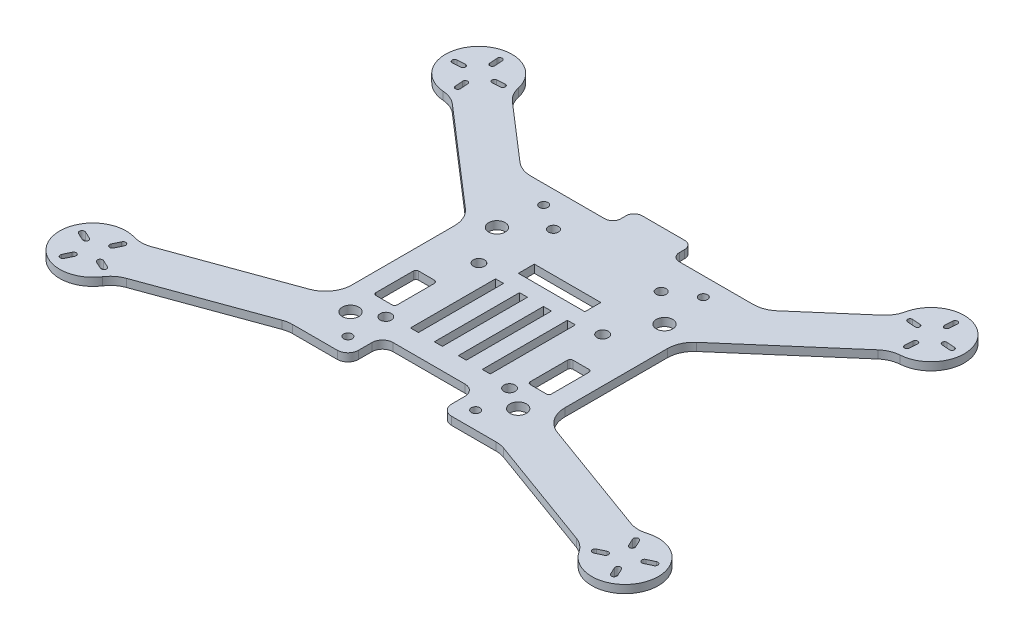
SolidWorks part; units mm, degrees
material "Thornel Mat VMA"
ref_plane "Front Plane" through (0, 0, 0) normal (0, 0, 1) x (1, 0, 0)
ref_plane "Top Plane" through (0, 0, 0) normal (0, 1, 0) x (1, 0, 0)
ref_plane "Right Plane" through (0, 0, 0) normal (1, 0, 0) x (0, 0, -1)
sketch "Sketch1" plane through (0, 0, 0) normal (0, 1, 0) x (1, 0, 0)
  line L0 (0, 0) -> (0, -25922.3753) construction
  line L1 (0, 0) -> (50000, 0) construction
  line L2 (0.0146, -0.0126) -> (37798.4826, -32730.3627) construction
  line L7 (-40, 24.0543) -> (-82.976, 61.2679)
  line L8 (-45.5212, 50) -> (-72.5023, 73.3634)
  line L9 (-0.0841, -0.0728) -> (-37798.5521, -32730.4229) construction
  line L10 (-40, -24.0543) -> (-82.976, -61.2679) construction
  line L11 (-45.5212, -50) -> (-72.5023, -73.3634) construction
  line L12 (45.5212, -50) -> (72.5023, -73.3634) construction
  line L13 (40, -24.0543) -> (82.976, -61.2679) construction
  line L14 (40, 24.0543) -> (82.976, 61.2679)
  line L15 (45.5212, 50) -> (72.5023, 73.3634)
  line L16 (-40, 24.0543) -> (-40, -24.0543) construction
  line L17 (-45.5212, 50) -> (45.5212, 50)
  line L18 (-45.5212, -50) -> (45.5212, -50) construction
  line L19 (40, 24.0543) -> (40, -24.0543) construction
  line L20 (10.4319, -16.2031) -> (-46974.1992, -17117.2103) construction
  line L21 (-10.0613, -15.3084) -> (45305.3281, -21146.2214) construction
  line L22 (-40, -26.0454) -> (-93.7107, -45.5945)
  line L23 (-40, 24.0543) -> (-40, -26.0454)
  line L24 (-40, -43.0722) -> (-88.2384, -60.6296)
  line L25 (-40, -43.0722) -> (40, -43.0722)
  line L26 (40, -43.0722) -> (88.2384, -60.6296)
  line L27 (40, -26.0454) -> (93.7107, -45.5945)
  line L28 (40, 24.0543) -> (40, -26.0454)
  arc A0 (-72.5023, 73.3634) -> (-82.976, 61.2679) centre (-85, 73.603) ccw
  arc A1 (82.976, 61.2679) -> (72.5023, 73.3634) centre (85, 73.603) ccw
  arc A2 (-82.976, -61.2679) -> (-72.5023, -73.3634) centre (-85, -73.603) ccw construction
  arc A3 (72.5023, -73.3634) -> (82.976, -61.2679) centre (85, -73.603) ccw construction
  arc A4 (-93.7107, -45.5945) -> (-88.2384, -60.6296) centre (-100, -56.397) ccw
  arc A5 (93.7107, -45.5945) -> (88.2384, -60.6296) centre (100, -56.397) cw
  point P44 (0, -43.0722)
  point P45 (0, -20)
  dimension "D2" = 25
  dimension "D3" = 16
  dimension "D1" = 170
  dimension "D4" = 130
  dimension "D5" = 40
  dimension "D6" = 50
  dimension "D7" = 70
  dimension "D8" = 65
  dimension "D9" = 16
  dimension "D10" = 100
  dimension "D11" = 20
extrude "Boss-Extrude1" add sketch "Sketch1" along normal blind 3
fillet "Fillet1" radius 10 8 edges at (45.5212, 1.5, -50) (-45.5212, 1.5, -50) (-40, 1.5, -24.0543) (40, 1.5, -24.0543) (40, 1.5, 26.0454) (40, 1.5, 43.0722) (-40, 1.5, 43.0722) (-40, 1.5, 26.0454)
fillet "Fillet2" radius 10 8 edges at (-72.5023, 1.5, -73.3634) (82.976, 1.5, -61.2679) (72.5023, 1.5, -73.3634) (-82.976, 1.5, -61.2679) (88.2384, 1.5, 60.6296) (93.7107, 1.5, 45.5945) (-93.7107, 1.5, 45.5945) (-88.2384, 1.5, 60.6296)
sketch "Sketch3" plane through (0, 3, 0) normal (0, 1, 0) x (1, 0, 0)
  line L0 (0, 0) -> (0, -50000) construction
  line L2 (-38.2367, -43.0722) -> (38.2367, -43.0722) construction
  circle A0 centre (-23.25, -23.0722) radius 2.11
  circle A1 centre (23.25, -23.0722) radius 2.11
  circle A2 centre (23.25, 11.9278) radius 2.11
  circle A3 centre (-23.25, 11.9278) radius 2.11
  dimension "D3" = 4.22
  dimension "D1" = 46.5
  dimension "D2" = 35
  dimension "D4" = 20
extrude "Cut-Extrude2" cut sketch "Sketch3" against normal through all
sketch "Sketch4" plane through (0, 3, 0) normal (0, 1, 0) x (1, 0, 0)
  line L0 (0, 0) -> (0, -50000) construction
  line L2 (-38.2367, -43.0722) -> (38.2367, -43.0722) construction
  circle A0 centre (-23.5, -36.0722) radius 1.1
  circle A1 centre (23.5, -36.0722) radius 1.1
  dimension "D3" = 2.2
  dimension "D1" = 47
  dimension "D2" = 7
extrude "Cut-Extrude3" [suppressed] cut sketch "Sketch4" against normal through all
sketch "Sketch5" plane through (0, 0, 0) normal (0, -1, 0) x (1, 0, 0)
  line L0 (0, -8.4275) -> (0, 49991.5725) construction
  line L1 (-11, 43.0722) -> (-11, 36.5722)
  line L3 (-11, 36.5722) -> (-4.5, 29.5722)
  line L4 (-4.5, 29.5722) -> (-4.5, 18.5722)
  line L5 (-4.5, 18.5722) -> (4.5, 18.5722)
  line L6 (-11, 43.0722) -> (11, 43.0722)
  line L7 (4.5, 29.5722) -> (4.5, 18.5722)
  line L8 (11, 36.5722) -> (4.5, 29.5722)
  line L9 (11, 43.0722) -> (11, 36.5722)
  line L10 (-38.2367, 43.0722) -> (38.2367, 43.0722) construction
  point P12 (0, 43.0722)
  point P13 (0, 18.5722)
  dimension "D1" = 11
  dimension "D2" = 6.5
  dimension "D3" = 24.5
  dimension "D4" = 11
  dimension "D5" = 4.5
extrude "Cut-Extrude4" [suppressed] cut sketch "Sketch5" against normal through all
sketch "Sketch6" plane through (0, 3, 0) normal (0, 1, 0) x (1, 0, 0)
  line L0 (0, 0) -> (0, -50000) construction
  line L2 (-38.2367, -43.0722) -> (38.2367, -43.0722) construction
  circle A0 centre (23.25, 25.9278) radius 2.11
  circle A1 centre (-23.25, 25.9278) radius 2.11
  circle A2 centre (-23.25, -9.0722) radius 2.11
  circle A3 centre (23.25, -9.0722) radius 2.11
  dimension "D3" = 4.22
  dimension "D1" = 46.5
  dimension "D2" = 35
  dimension "D4" = 34
extrude "Cut-Extrude5" [suppressed] cut sketch "Sketch6" against normal through all
sketch "Sketch7" plane through (0, 0, 0) normal (0, -1, 0) x (1, 0, 0)
  line L0 (0, 0) -> (0, -50000) construction
  line L1 (-17.5, 43.0722) -> (-17.5, 30.0722)
  line L2 (-38.2367, 43.0722) -> (38.2367, 43.0722) construction
  line L3 (-17.5, 30.0722) -> (17.5, 30.0722)
  line L4 (17.5, 30.0722) -> (17.5, 43.0722)
  line L5 (17.5, 43.0722) -> (-17.5, 43.0722)
  dimension "D1" = 35
  dimension "D2" = 13
extrude "Cut-Extrude6" cut sketch "Sketch7" against normal through all
fillet "Fillet3" radius 4 4 edges at (17.5, 1.5, 30.0722) (17.5, 1.5, 43.0722) (-17.5, 1.5, 30.0722) (-17.5, 1.5, 43.0722)
sketch "Sketch8" plane through (0, 3, 0) normal (0, 1, 0) x (1, 0, 0)
  line L0 (0, 0) -> (0, -50000) construction
  line L1 (-38.2367, -43.0722) -> (-21.5, -43.0722) construction
  circle A0 centre (-31.5, -28.0722) radius 3.1
  circle A1 centre (31.5, -28.0722) radius 3.1
  circle A2 centre (-31.5, 26.9278) radius 3.1
  circle A3 centre (31.5, 26.9278) radius 3.1
  dimension "D1" = 6.2
  dimension "D2" = 63
  dimension "D3" = 55
  dimension "D4" = 15
extrude "Cut-Extrude7" cut sketch "Sketch8" against normal through all
sketch "Sketch9" plane through (0, 3, 0) normal (0, 1, 0) x (1, 0, 0)
  line L0 (0, -0.8752) -> (0, -50000.8752) construction
  line L1 (-38.2367, -43.0722) -> (-21.5, -43.0722) construction
  circle A0 centre (-20.25, 36.9278) radius 1.875
  circle A1 centre (20.25, 36.9278) radius 1.875
  dimension "D1" = 3.75
  dimension "D2" = 40.5
  dimension "D3" = 80
extrude "Cut-Extrude8" cut sketch "Sketch9" against normal through all
sketch "Sketch10" plane through (0, 3, 0) normal (0, 1, 0) x (1, 0, 0)
  line L0 (41.7933, 50) -> (-41.7933, 50) construction
  line L1 (-11, 50) -> (11, 50)
  line L2 (-11, 50) -> (-11, 58)
  line L3 (-11, 58) -> (11, 58)
  line L4 (11, 50) -> (11, 58)
  point P6 (0, 58)
  dimension "D1" = 22
  dimension "D2" = 8
extrude "Boss-Extrude2" add sketch "Sketch10" against normal up to surface (3 mm away) up to face at (-20.25, 0, -35.0528)
fillet "Fillet4" radius 3 4 edges at (11, 1.5, -50) (11, 1.5, -58) (-11, 1.5, -58) (-11, 1.5, -50)
sketch "Sketch11" plane through (0, 3, 0) normal (0, 1, 0) x (1, 0, 0)
  line L0 (0, 0) -> (0, -50000) construction
  line L1 (-33, -2) -> (-25, -2)
  line L2 (-33, -2) -> (-33, -18)
  line L3 (-33, -18) -> (-25, -18)
  line L4 (-25, -2) -> (-25, -18)
  line L5 (25, -2) -> (25, -18)
  line L6 (33, -18) -> (25, -18)
  line L7 (33, -2) -> (33, -18)
  line L8 (33, -2) -> (25, -2)
  dimension "D1" = 8
  dimension "D2" = 16
  dimension "D3" = 25
  dimension "D4" = 2
extrude "Cut-Extrude9" cut sketch "Sketch11" against normal through all
fillet "Fillet5" radius 1 8 edges at (33, 1.5, 18) (25, 1.5, 18) (25, 1.5, 2) (33, 1.5, 2) (-25, 1.5, 18) (-33, 1.5, 18) (-33, 1.5, 2) (-25, 1.5, 2)
sketch "Sketch12" plane through (0, 3, 0) normal (0, 1, 0) x (1, 0, 0)
  line L0 (0, 0) -> (0, -50000) construction
  line L1 (-38.2367, -43.0722) -> (-21.5, -43.0722) construction
  circle A0 centre (-30, 43) radius 1.6
  circle A1 centre (30, 43) radius 1.6
  circle A2 centre (-24, -36.5722) radius 1.6
  circle A3 centre (24, -36.5722) radius 1.6
  dimension "D1" = 3.2
  dimension "D2" = 60
  dimension "D3" = 43
  dimension "D4" = 6.5
  dimension "D5" = 24
extrude "Cut-Extrude10" cut sketch "Sketch12" against normal through all
sketch "Sketch13" plane through (0, 3, 0) normal (0, 1, 0) x (1, 0, 0)
  line L0 (0, 0) -> (0, -50000) construction
  line L1 (-13.5, -30.0722) -> (13.5, -30.0722) construction
  line L2 (-15, 9.9278) -> (-12, 9.9278)
  line L3 (-15, 9.9278) -> (-15, -22.0722)
  line L4 (-15, -22.0722) -> (-12, -22.0722)
  line L5 (-12, 9.9278) -> (-12, -22.0722)
  line L6 (-6, 9.9278) -> (-6, -22.0722)
  line L7 (-6, 9.9278) -> (-3, 9.9278)
  line L8 (-3, 9.9278) -> (-3, -22.0722)
  line L9 (-6, -22.0722) -> (-3, -22.0722)
  line L10 (3, 9.9278) -> (3, -22.0722)
  line L11 (3, 9.9278) -> (6, 9.9278)
  line L12 (6, 9.9278) -> (6, -22.0722)
  line L13 (3, -22.0722) -> (6, -22.0722)
  line L14 (12, 9.9278) -> (12, -22.0722)
  line L15 (12, 9.9278) -> (15, 9.9278)
  line L16 (15, 9.9278) -> (15, -22.0722)
  line L17 (12, -22.0722) -> (15, -22.0722)
  dimension "D1" = 3
  dimension "D2" = 15
  dimension "D3" = 32
  dimension "D4" = 8
  dimension "D6" = 9
  dimension "D5" = 4
extrude "Cut-Extrude11" cut sketch "Sketch13" against normal through all
sketch "Sketch14" plane through (0, 3, 0) normal (0, 1, 0) x (1, 0, 0)
  line L0 (-80.023, 69.2933) -> (37643.1982, -32595.8992) construction
  line L1 (-48.3393, 52.4403) -> (-69.5576, 70.8135) construction
  line L2 (-85.6092, 82.0811) -> (-84.3908, 65.1248) construction
  line L3 (-93.4781, 72.9937) -> (-76.5219, 74.2122) construction
  line L4 (-85.6092, 82.0811) -> (-85.3942, 79.0888) construction
  line L5 (-84.7115, 82.1456) -> (-84.4965, 79.1533)
  line L6 (-86.5069, 82.0166) -> (-86.2919, 79.0243)
  line L7 (-93.4781, 72.9937) -> (-90.4859, 73.2088) construction
  line L8 (-93.5426, 73.8914) -> (-90.5504, 74.1065)
  line L9 (-93.4136, 72.0961) -> (-90.4213, 72.3111)
  line L10 (-84.3908, 65.1248) -> (-84.6058, 68.1171) construction
  line L11 (-83.4931, 65.1893) -> (-83.7081, 68.1816)
  line L12 (-85.2885, 65.0603) -> (-85.5035, 68.0526)
  line L13 (-76.5219, 74.2122) -> (-79.5141, 73.9972) construction
  line L14 (-76.5864, 75.1099) -> (-79.5787, 74.8949)
  line L15 (-76.4574, 73.3145) -> (-79.4496, 73.0995)
  line L16 (0, 0) -> (0, -50000) construction
  line L17 (85.6092, 82.0811) -> (85.3942, 79.0888) construction
  line L18 (84.7115, 82.1456) -> (84.4965, 79.1533)
  line L19 (86.5069, 82.0166) -> (86.2919, 79.0243)
  line L20 (93.4781, 72.9937) -> (90.4859, 73.2088) construction
  line L21 (93.5426, 73.8914) -> (90.5504, 74.1065)
  line L22 (93.4136, 72.0961) -> (90.4213, 72.3111)
  line L23 (84.3908, 65.1248) -> (84.6058, 68.1171) construction
  line L24 (83.4931, 65.1893) -> (83.7081, 68.1816)
  line L25 (85.2885, 65.0603) -> (85.5035, 68.0526)
  line L26 (76.5219, 74.2122) -> (79.5141, 73.9972) construction
  line L27 (76.5864, 75.1099) -> (79.5787, 74.8949)
  line L28 (76.4574, 73.3145) -> (79.4496, 73.0995)
  line L29 (93.4781, 72.9937) -> (76.5219, 74.2122) construction
  line L30 (85.6092, 82.0811) -> (84.3908, 65.1248) construction
  line L31 (-92.9602, -53.8347) -> (46712.8802, 16982.0979) construction
  line L32 (-46.5798, -28.4402) -> (-90.0503, -44.2622) construction
  line L33 (-96.4077, -48.6934) -> (-103.5923, -64.1006) construction
  line L34 (-107.7036, -52.8048) -> (-92.2964, -59.9893) construction
  line L35 (-96.4077, -48.6934) -> (-97.6756, -51.4123) construction
  line L36 (-95.5014, -49.116) -> (-96.7693, -51.8349)
  line L37 (-97.3141, -48.2708) -> (-98.5819, -50.9897)
  line L38 (-103.5923, -64.1006) -> (-102.3244, -61.3817) construction
  line L39 (-102.6859, -64.5233) -> (-101.4181, -61.8043)
  line L40 (-104.4986, -63.678) -> (-103.2307, -60.9591)
  line L41 (-107.7036, -52.8048) -> (-104.9847, -54.0726) construction
  line L42 (-107.281, -51.8985) -> (-104.5621, -53.1663)
  line L43 (-108.1262, -53.7111) -> (-105.4073, -54.9789)
  line L44 (-92.2964, -59.9893) -> (-95.0153, -58.7214) construction
  line L45 (-91.8738, -59.083) -> (-94.5927, -57.8151)
  line L46 (-92.719, -60.8956) -> (-95.4379, -59.6277)
  line L47 (96.4077, -48.6934) -> (97.6756, -51.4123) construction
  line L48 (95.5014, -49.116) -> (96.7693, -51.8349)
  line L49 (97.3141, -48.2708) -> (98.5819, -50.9897)
  line L50 (103.5923, -64.1006) -> (102.3244, -61.3817) construction
  line L51 (102.6859, -64.5233) -> (101.4181, -61.8043)
  line L52 (104.4986, -63.678) -> (103.2307, -60.9591)
  line L53 (107.7036, -52.8048) -> (104.9847, -54.0726) construction
  line L54 (107.281, -51.8985) -> (104.5621, -53.1663)
  line L55 (108.1262, -53.7111) -> (105.4073, -54.9789)
  line L56 (92.2964, -59.9893) -> (95.0153, -58.7214) construction
  line L57 (91.8738, -59.083) -> (94.5927, -57.8151)
  line L58 (92.719, -60.8956) -> (95.4379, -59.6277)
  line L59 (107.7036, -52.8048) -> (92.2964, -59.9893) construction
  line L60 (96.4077, -48.6934) -> (103.5923, -64.1006) construction
  arc A0 (-84.7115, 82.1456) -> (-86.5069, 82.0166) centre (-85.6092, 82.0811) ccw
  arc A1 (-86.2919, 79.0243) -> (-84.4965, 79.1533) centre (-85.3942, 79.0888) ccw
  arc A2 (-93.5426, 73.8914) -> (-93.4136, 72.0961) centre (-93.4781, 72.9937) ccw
  arc A3 (-90.4213, 72.3111) -> (-90.5504, 74.1065) centre (-90.4859, 73.2088) ccw
  arc A4 (-83.4931, 65.1893) -> (-85.2885, 65.0603) centre (-84.3908, 65.1248) cw
  arc A5 (-85.5035, 68.0526) -> (-83.7081, 68.1816) centre (-84.6058, 68.1171) cw
  arc A6 (-76.5864, 75.1099) -> (-76.4574, 73.3145) centre (-76.5219, 74.2122) cw
  arc A7 (-79.4496, 73.0995) -> (-79.5787, 74.8949) centre (-79.5141, 73.9972) cw
  arc A8 (84.7115, 82.1456) -> (86.5069, 82.0166) centre (85.6092, 82.0811) cw
  arc A9 (86.2919, 79.0243) -> (84.4965, 79.1533) centre (85.3942, 79.0888) cw
  arc A10 (93.5426, 73.8914) -> (93.4136, 72.0961) centre (93.4781, 72.9937) cw
  arc A11 (90.4213, 72.3111) -> (90.5504, 74.1065) centre (90.4859, 73.2088) cw
  arc A12 (83.4931, 65.1893) -> (85.2885, 65.0603) centre (84.3908, 65.1248) ccw
  arc A13 (85.5035, 68.0526) -> (83.7081, 68.1816) centre (84.6058, 68.1171) ccw
  arc A14 (76.5864, 75.1099) -> (76.4574, 73.3145) centre (76.5219, 74.2122) ccw
  arc A15 (79.4496, 73.0995) -> (79.5787, 74.8949) centre (79.5141, 73.9972) ccw
  arc A16 (-95.5014, -49.116) -> (-97.3141, -48.2708) centre (-96.4077, -48.6934) ccw
  arc A17 (-98.5819, -50.9897) -> (-96.7693, -51.8349) centre (-97.6756, -51.4123) ccw
  arc A18 (-102.6859, -64.5233) -> (-104.4986, -63.678) centre (-103.5923, -64.1006) cw
  arc A19 (-103.2307, -60.9591) -> (-101.4181, -61.8043) centre (-102.3244, -61.3817) cw
  arc A20 (-107.281, -51.8985) -> (-108.1262, -53.7111) centre (-107.7036, -52.8048) ccw
  arc A21 (-105.4073, -54.9789) -> (-104.5621, -53.1663) centre (-104.9847, -54.0726) ccw
  arc A22 (-91.8738, -59.083) -> (-92.719, -60.8956) centre (-92.2964, -59.9893) cw
  arc A23 (-95.4379, -59.6277) -> (-94.5927, -57.8151) centre (-95.0153, -58.7214) cw
  arc A24 (95.5014, -49.116) -> (97.3141, -48.2708) centre (96.4077, -48.6934) cw
  arc A25 (98.5819, -50.9897) -> (96.7693, -51.8349) centre (97.6756, -51.4123) cw
  arc A26 (102.6859, -64.5233) -> (104.4986, -63.678) centre (103.5923, -64.1006) ccw
  arc A27 (103.2307, -60.9591) -> (101.4181, -61.8043) centre (102.3244, -61.3817) ccw
  arc A28 (107.281, -51.8985) -> (108.1262, -53.7111) centre (107.7036, -52.8048) cw
  arc A29 (105.4073, -54.9789) -> (104.5621, -53.1663) centre (104.9847, -54.0726) cw
  arc A30 (91.8738, -59.083) -> (92.719, -60.8956) centre (92.2964, -59.9893) ccw
  arc A31 (95.4379, -59.6277) -> (94.5927, -57.8151) centre (95.0153, -58.7214) ccw
  point P7 (-85, 73.603)
  point P11 (-85, 73.603)
  point P15 (-85.5017, 80.585)
  point P20 (-91.982, 73.1013)
  point P30 (-84.4983, 66.621)
  point P37 (-78.018, 74.1047)
  point P52 (85.5017, 80.585)
  point P59 (91.982, 73.1013)
  point P66 (84.4983, 66.621)
  point P73 (78.018, 74.1047)
  point P85 (-100, -56.397)
  point P87 (-100, -56.397)
  point P89 (-97.0417, -50.0529)
  point P96 (-102.9583, -62.7412)
  point P102 (-106.3442, -53.4387)
  point P109 (-93.6558, -59.3554)
  point P116 (97.0417, -50.0529)
  point P123 (102.9583, -62.7412)
  point P130 (106.3442, -53.4387)
  point P137 (93.6558, -59.3554)
  dimension "D5" = 1.8
  dimension "D1" = 45
  dimension "D2" = 17
  dimension "D3" = 17
  dimension "D4" = 3
  dimension "D6" = 1.8
  dimension "D7" = 17
  dimension "D8" = 45
  dimension "D9" = 2
  dimension "D10" = 3
  dimension "D11" = 2
extrude "Cut-Extrude12" cut sketch "Sketch14" against normal through all and the other way through all
sketch "Sketch15" plane through (0, 3, 0) normal (0, 1, 0) x (1, 0, 0)
  line L1 (-12.5, 22) -> (12.5, 22)
  line L2 (-12.5, 22) -> (-12.5, 16)
  line L3 (-12.5, 16) -> (12.5, 16)
  line L4 (12.5, 22) -> (12.5, 16)
  point P4 (0, 22)
  dimension "D1" = 25
  dimension "D2" = 6
  dimension "D3" = 16
extrude "Cut-Extrude13" cut sketch "Sketch15" against normal through all
